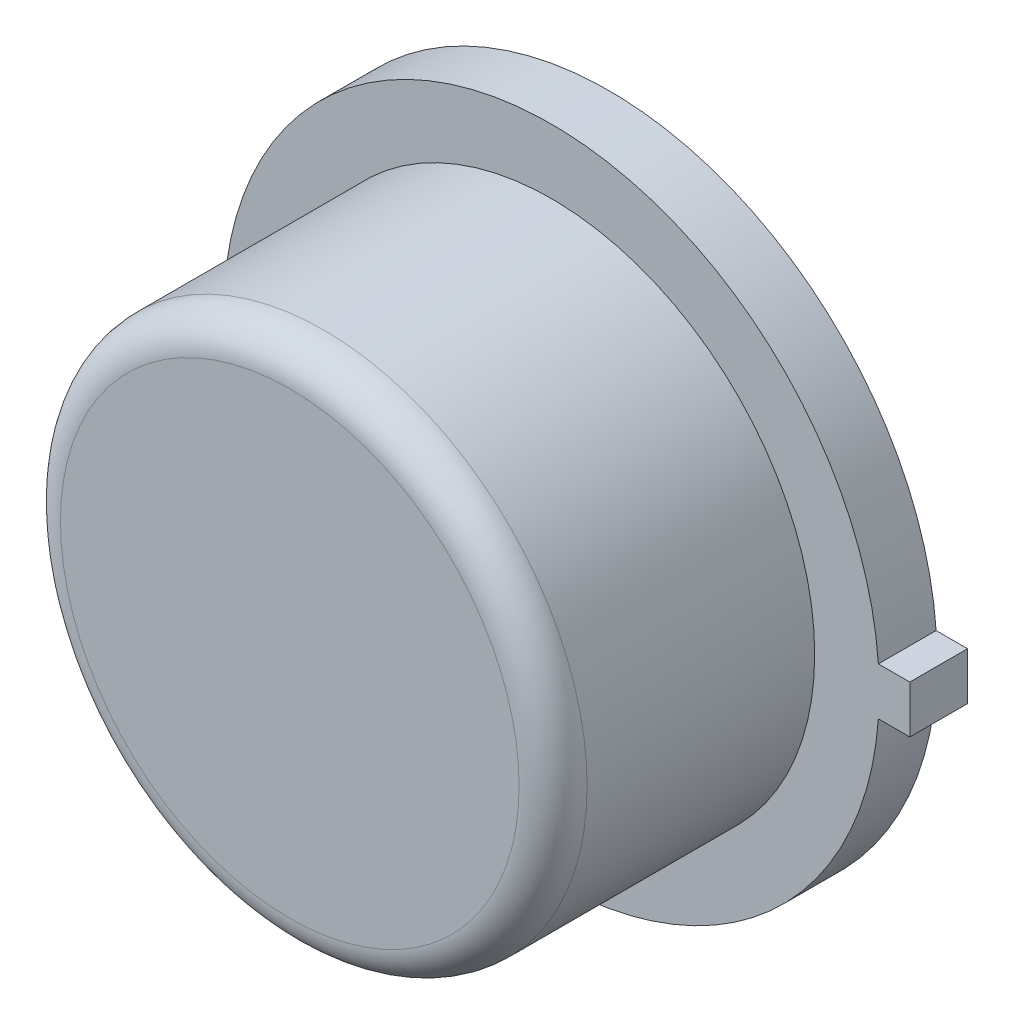
SolidWorks part; units mm, degrees
ref_plane "Front Plane" through (0, 0, 0) normal (0, 0, 1) x (1, 0, 0)
ref_plane "Top Plane" through (0, 0, 0) normal (0, 1, 0) x (1, 0, 0)
ref_plane "Right Plane" through (0, 0, 0) normal (1, 0, 0) x (0, 0, -1)
sketch "Sketch1" plane through (0, 0, 0) normal (0, 0, 1) x (1, 0, 0)
  line L1 (2.4511, 0.1778) -> (2.6797, 0.1778)
  line L3 (2.4511, -0.1778) -> (2.6797, -0.1778)
  line L4 (2.6797, 0.1778) -> (2.6797, -0.1778)
  line L5 (2.4511, 0.1778) -> (2.4444, 0.1778)
  line L6 (2.4511, -0.1778) -> (2.4446, -0.1778)
  arc A0 (2.4446, 0.1778) -> (2.4446, -0.1778) centre (0, 0) ccw
  dimension "D1" = 4.9022
  dimension "D2" = 0.3556
  dimension "D3" = 0.2286
extrude "Boss-Extrude1" add sketch "Sketch1" along normal blind 0.4318
sketch "Sketch2" plane through (0, 0, 0.4318) normal (0, 0, 1) x (1, 0, 0)
  circle A0 centre (0, 0) radius 1.9685
  dimension "D1" = 3.937
extrude "Boss-Extrude2" add sketch "Sketch2" along normal blind 1.9558
sketch "Sketch3" plane through (0, 0, 0) normal (0, 0, -1) x (-1, 0, 0)
  circle A0 centre (0, 0) radius 1.7576
extrude "Boss-Extrude3" add sketch "Sketch3" along normal blind 0.0025
fillet "Fillet1" radius 0.254 1 edges at (1.9685, 0, 2.3876)
